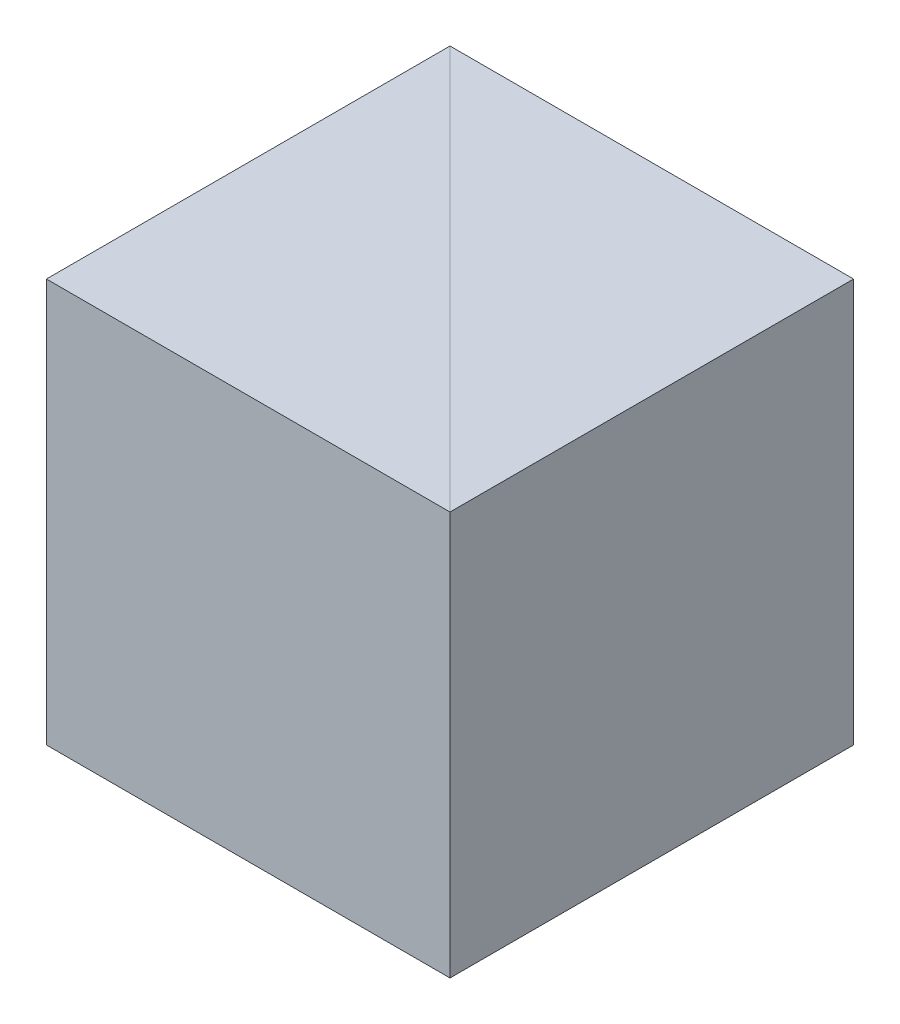
SolidWorks part; units mm, degrees
ref_plane "前视基准面" through (0, 0, 0) normal (0, 0, 1) x (1, 0, 0)
ref_plane "上视基准面" through (0, 0, 0) normal (0, 1, 0) x (1, 0, 0)
ref_plane "右视基准面" through (0, 0, 0) normal (1, 0, 0) x (0, 0, -1)
sketch "草图1" plane through (0, 0, 0) normal (0, 1, 0) x (1, 0, 0)
  line L0 (0, 0) -> (0, 12.5)
  line L1 (0, 12.5) -> (-12.5, 12.5)
  line L2 (-12.5, 12.5) -> (0, 0)
  dimension "D1" = 12.5
  dimension "D2" = 12.5
extrude "凸台-拉伸1" add sketch "草图1" along normal blind 12.5
sketch "草图2" plane through (0, 0, 0) normal (0, -1, 0) x (1, 0, 0)
  line L0 (-12.5, -12.5) -> (-12.5, 0)
  line L1 (-12.5, 0) -> (0, 0)
  line L2 (0, 0) -> (-12.5, -12.5)
extrude "凸台-拉伸2" add sketch "草图2" against normal blind 12.5 separate body
